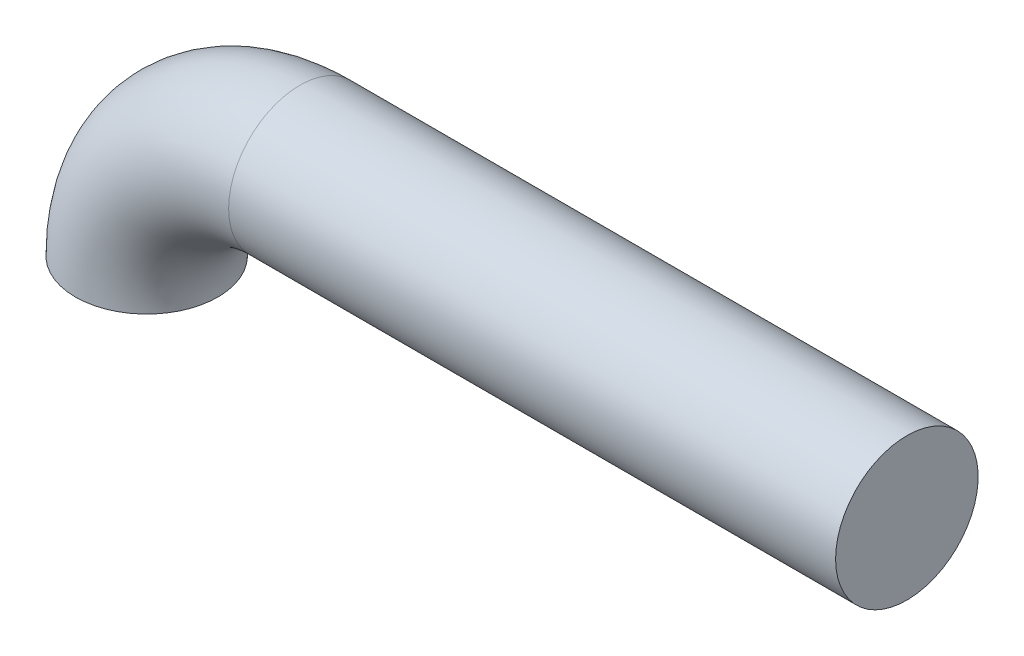
SolidWorks part; units mm, degrees
ref_plane "Спереди" through (0, 0, 0) normal (0, 0, 1) x (1, 0, 0)
ref_plane "Сверху" through (0, 0, 0) normal (0, 1, 0) x (1, 0, 0)
ref_plane "Справа" through (0, 0, 0) normal (1, 0, 0) x (0, 0, -1)
sketch "Эскиз1" plane through (0, 0, 0) normal (0, 1, 0) x (1, 0, 0)
  circle A0 centre (0, 0) radius 60
  dimension "D1" = 120
sketch "Эскиз2" plane through (0, 0, 0) normal (0, 0, 1) x (1, 0, 0)
  line L0 (129, 129) -> (640, 129)
  arc A0 (0, 0) -> (129, 129) centre (129, 0) cw
  point P3 (0, 0)
  dimension "D1" = 129
  dimension "D2" = 640
sweep "По траектории1" add profiles "Эскиз1" path "Эскиз2"
